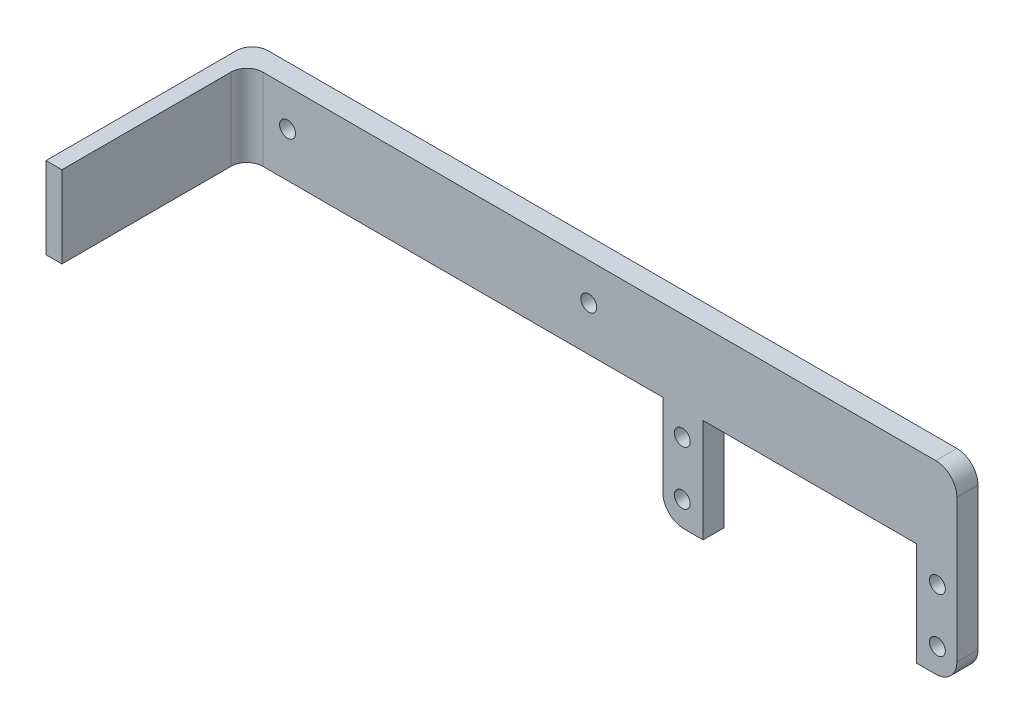
SolidWorks part; units mm, degrees
material "Acrylic (Medium-high impact)"
ref_plane "Front Plane" through (0, 0, 0) normal (0, 0, 1) x (1, 0, 0)
ref_plane "Top Plane" through (0, 0, 0) normal (0, 1, 0) x (1, 0, 0)
ref_plane "Right Plane" through (0, 0, 0) normal (1, 0, 0) x (0, 0, -1)
sketch "Sketch2" plane through (0, 0, 0) normal (0, 0, 1) x (1, 0, 0)
  line L0 (-67.0811, 16.9235) -> (-26.6951, 16.9235)
  line L1 (-26.6951, 16.9235) -> (-26.6951, -2.6345)
  line L2 (-26.6951, -2.6345) -> (-19.0751, -2.6345)
  line L3 (-19.0751, -2.6345) -> (-19.0751, 32.3655)
  line L4 (-19.0751, 32.3655) -> (-67.0811, 32.3655)
  line L6 (-74.7011, 16.9235) -> (-74.7011, -2.6345)
  line L7 (-74.7011, -2.6345) -> (-67.0811, -2.6345)
  line L8 (-67.0811, -2.6345) -> (-67.0811, 16.9235)
  line L9 (-67.0811, 16.9235) -> (-67.1703, 16.7363)
  line L10 (-74.7011, 32.3655) -> (-67.0811, 32.3655)
  line L11 (-159.7011, 16.9235) -> (-74.7011, 16.9235)
  line L12 (-159.3598, 32.8744) -> (-156.3911, 32.8744)
  line L13 (-159.3598, 32.8744) -> (-159.3598, 16.9235)
  line L14 (-159.3598, 16.9235) -> (-156.3911, 16.9235)
  line L15 (-156.3911, 32.8744) -> (-156.3911, 16.9235)
  line L17 (-159.7011, 16.9235) -> (-159.7011, 32.3655)
  line L23 (-159.7011, 32.3655) -> (-74.7011, 32.3655)
  line L24 (-159.7011, 32.3655) -> (-159.3598, 32.8744)
extrude "Boss-Extrude2" add sketch "Sketch2" along normal blind 4
fillet "Fillet1" radius 4 3 edges at (-74.7011, -2.6345, 2) (-19.0751, -2.6345, 2) (-19.0751, 32.3655, 2)
sketch "Sketch3" plane through (0, 0, 4) normal (0, 0, 1) x (1, 0, 0)
  line L4 (-74.7011, 16.9235) -> (-74.7011, 1.3655) construction
  circle A0 centre (-145.7011, 25.3655) radius 1.5
  circle A1 centre (-88.7011, 25.3655) radius 1.5
  dimension "D3" = 14
sketch "Sketch6" plane through (0, 0, 4) normal (0, 0, 1) x (1, 0, 0)
  line L0 (-67.0811, -2.6345) -> (-67.0811, 16.9235) construction
  line L3 (-67.0811, 16.9235) -> (-26.6951, 16.9235) construction
  circle A4 centre (-71.0181, 12.2245) radius 1.5
  circle A5 centre (-22.7581, 12.2245) radius 1.5
  circle A6 centre (-22.7581, 2.0645) radius 1.5
  circle A7 centre (-71.0181, 2.0645) radius 1.5
  dimension "D5" = 3.937
  dimension "D6" = 4.699
  dimension "D7" = 2
  dimension "D8" = 2
extrude "Cut-Extrude1" cut sketch "Sketch6" against normal blind 4
extrude "Cut-Extrude2" cut sketch "Sketch3" against normal blind 4 contours A0 | A1
sketch "Sketch7" plane through (0, 0, 4) normal (0, 0, 1) x (1, 0, 0)
  line L0 (-156.3911, 16.9235) -> (-74.7011, 16.9235) construction
  line L1 (-156.3911, 32.3655) -> (-153.3845, 32.3655)
  line L2 (-156.3911, 32.3655) -> (-156.3911, 16.9235)
  line L3 (-156.3911, 16.9235) -> (-153.3845, 16.9235)
  line L4 (-153.3845, 32.3655) -> (-153.3845, 16.9235)
extrude "Boss-Extrude3" add sketch "Sketch7" along normal blind 35
fillet "Fillet2" radius 3 1 edges at (-153.3845, 24.6445, 4)
fillet "Fillet3" radius 3 1 edges at (-156.3911, 24.6445, 0)
